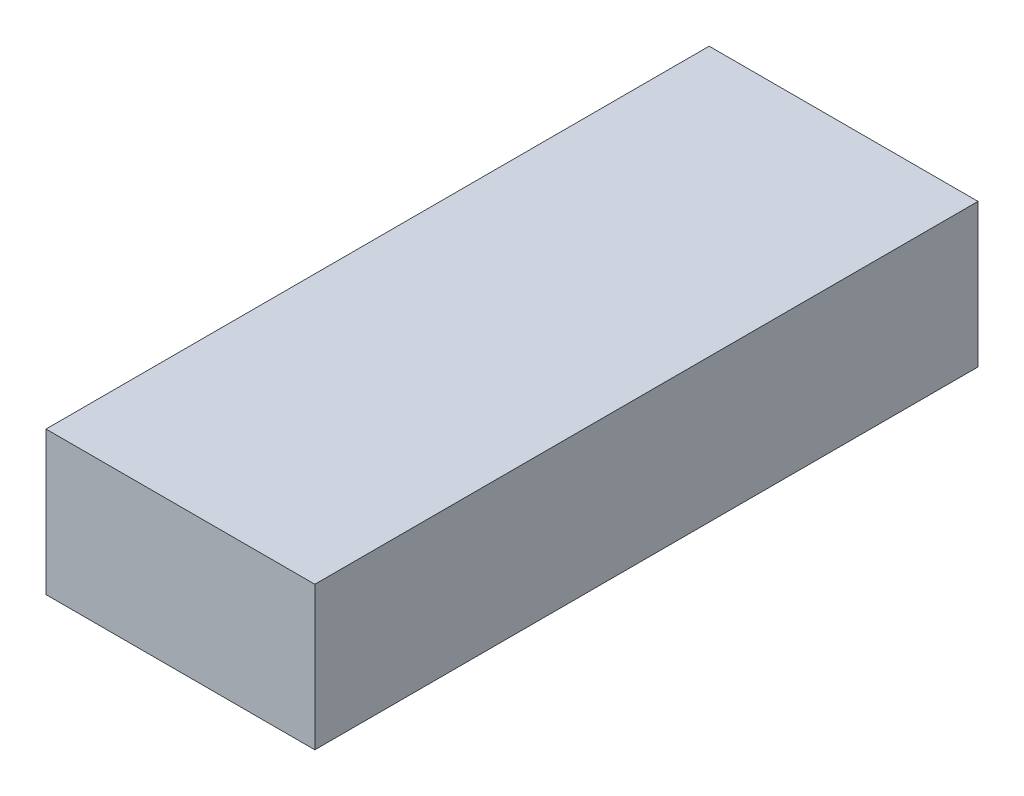
SolidWorks part; units mm, degrees
ref_plane "Front Plane" through (0, 0, 0) normal (0, 0, 1) x (1, 0, 0)
ref_plane "Top Plane" through (0, 0, 0) normal (0, 1, 0) x (1, 0, 0)
ref_plane "Right Plane" through (0, 0, 0) normal (1, 0, 0) x (0, 0, -1)
sketch "Sketch1" plane through (0, 0, 0) normal (0, 1, 0) x (1, 0, 0)
  line L1 (0, 0) -> (15, 0)
  line L2 (0, 0) -> (0, 37)
  line L3 (0, 37) -> (15, 37)
  line L4 (15, 0) -> (15, 37)
extrude "Boss-Extrude1" add sketch "Sketch1" along normal blind 8
